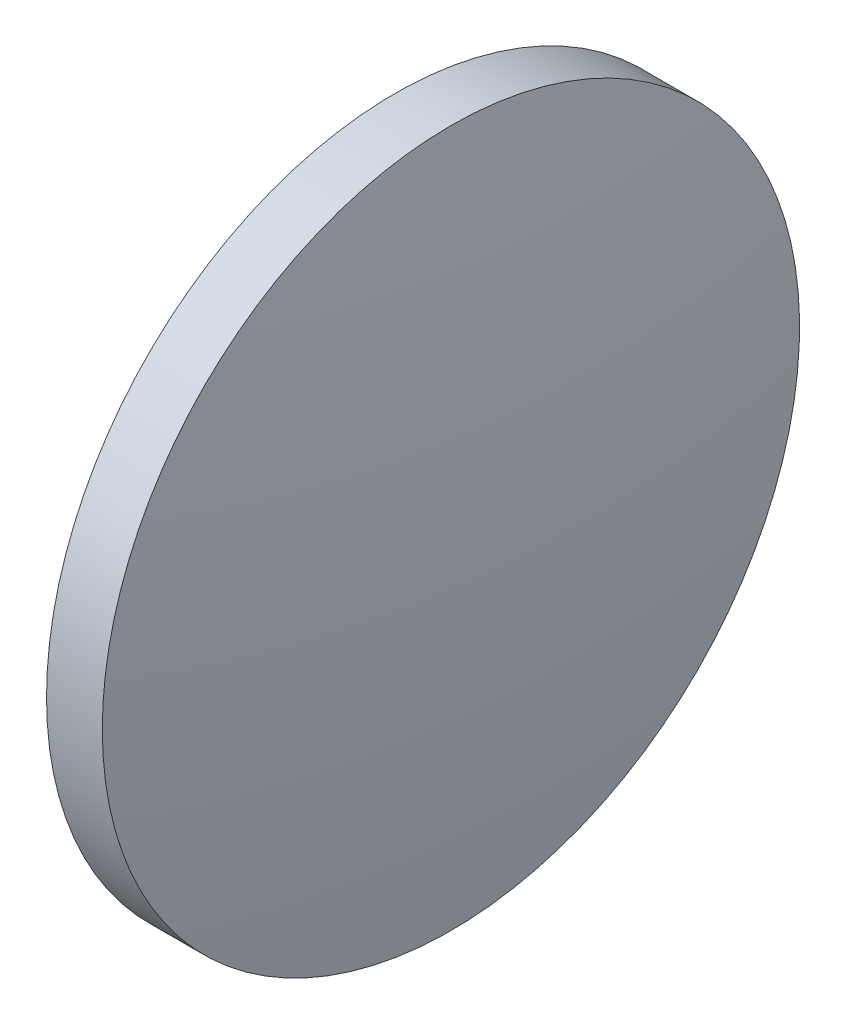
SolidWorks part; units mm, degrees
ref_plane "前视基准面" through (0, 0, 0) normal (0, 0, 1) x (1, 0, 0)
ref_plane "上视基准面" through (0, 0, 0) normal (0, 1, 0) x (1, 0, 0)
ref_plane "右视基准面" through (0, 0, 0) normal (1, 0, 0) x (0, 0, -1)
sketch "草图1" plane through (0, 0, 0) normal (0, 0, 1) x (1, 0, 0)
  line L0 (1224.206, 317.4353) -> (1237.6518, 317.4353) construction
  line L1 (1228.9481, 317.4353) -> (1228.9481, 329.9353)
  line L2 (1231.8981, 317.4353) -> (1228.9481, 317.4353)
  line L5 (1228.9481, 329.9353) -> (1230.9481, 329.9353)
  arc A0 (1231.8981, 317.4353) -> (1230.9481, 329.9353) centre (1149.1862, 317.4353) ccw
revolve "旋转1" add sketch "草图1" angle 360 about L0
